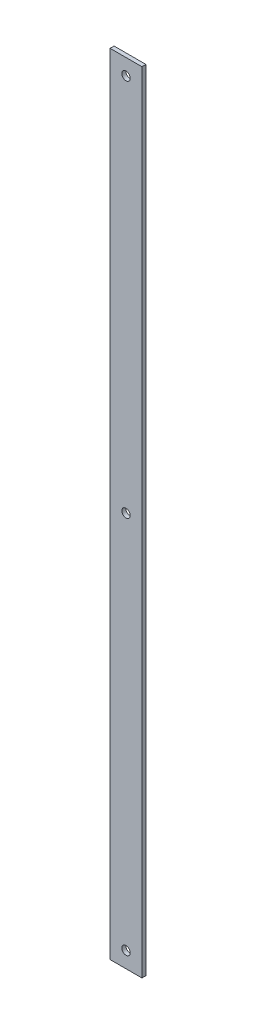
SolidWorks part; units mm, degrees
material "PC High Viscosity"
ref_plane "Front Plane" through (0, 0, 0) normal (0, 0, 1) x (1, 0, 0)
ref_plane "Top Plane" through (0, 0, 0) normal (0, 1, 0) x (1, 0, 0)
ref_plane "Right Plane" through (0, 0, 0) normal (1, 0, 0) x (0, 0, -1)
sketch "Sketch1" plane through (0, 0, 0) normal (0, 0, 1) x (1, 0, 0)
  line L1 (0, 0) -> (-25.4, 0)
  line L2 (0, 0) -> (0, 628.65)
  line L3 (0, 628.65) -> (-25.4, 628.65)
  line L4 (-25.4, 0) -> (-25.4, 628.65)
  dimension "D1" = 25.4
  dimension "D2" = 628.65
extrude "Boss-Extrude1" add sketch "Sketch1" along normal blind 3.175
sketch "Sketch2" plane through (0, 0, 3.175) normal (0, 0, 1) x (1, 0, 0)
  line L0 (-25.4, 628.65) -> (-25.4, 0) construction
  line L1 (-25.4, 0) -> (0, 0) construction
  circle A0 centre (-12.7, 12.7) radius 3.3655
  dimension "D1" = 6.731
  dimension "D2" = 12.7
  dimension "D3" = 12.7
extrude "Cut-Extrude1" cut sketch "Sketch2" against normal through all
pattern_linear "LPattern1" count 3 spacing 301.625 along (0, 1, 0) of "Cut-Extrude1"
